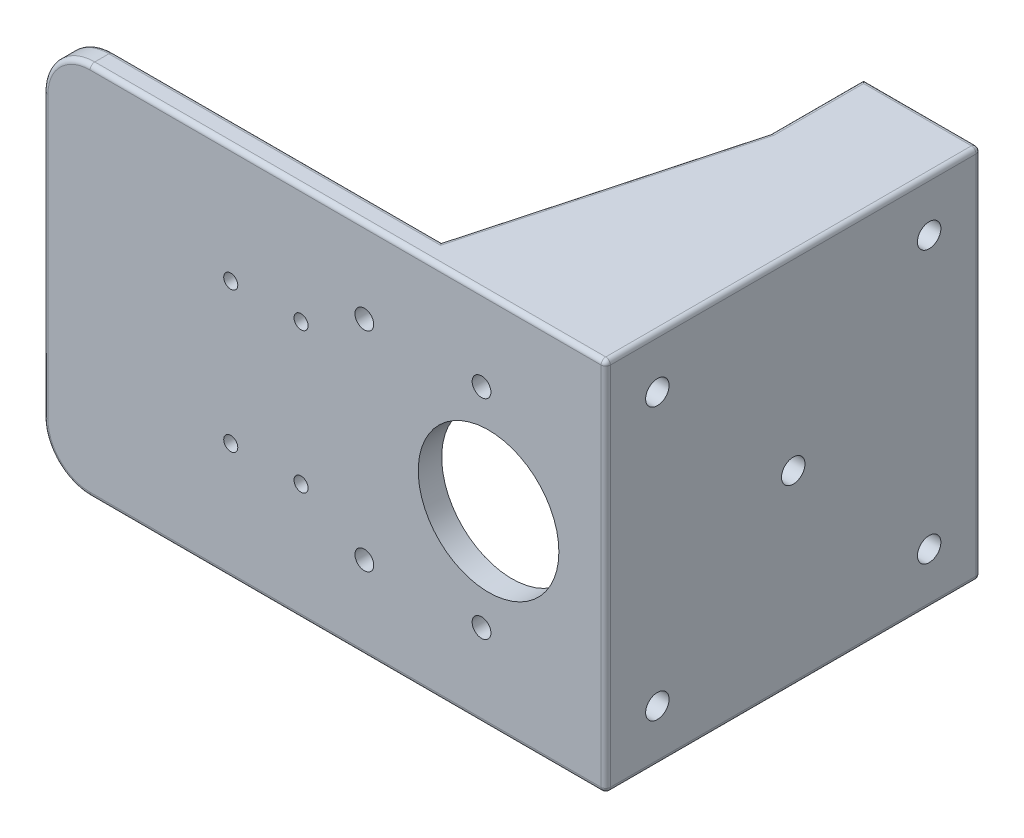
SolidWorks part; units mm, degrees
ref_plane "前视基准面" through (0, 0, 0) normal (0, 0, 1) x (1, 0, 0)
ref_plane "上视基准面" through (0, 0, 0) normal (0, 1, 0) x (1, 0, 0)
ref_plane "右视基准面" through (0, 0, 0) normal (1, 0, 0) x (0, 0, -1)
sketch "草图1" plane through (0, 0, 0) normal (0, 0, 1) x (1, 0, 0)
  line L1 (60, -40) -> (-60, -40)
  line L2 (60, -40) -> (60, 40)
  line L3 (60, 40) -> (-60, 40)
  line L4 (-60, -40) -> (-60, 40)
  line L5 (60, -40) -> (-60, 40) construction
  line L6 (60, 40) -> (-60, -40) construction
  point P0 (0, 0)
  dimension "D1" = 80
  dimension "D2" = 120
extrude "凸台-拉伸1" add sketch "草图1" along normal blind 5
sketch "草图3" plane through (0, 0, 5) normal (0, 0, 1) x (1, 0, 0)
  circle A0 centre (-45, 0) radius 4
  dimension "D2" = 8
extrude "切除-拉伸2" cut sketch "草图3" against normal blind 10
sketch "草图4" plane through (0, 0, 5) normal (0, 0, 1) x (1, 0, 0)
  line L1 (102, -10) -> (14, -10)
  line L2 (102, -10) -> (102, 10)
  line L3 (102, 10) -> (14, 10)
  line L4 (14, -10) -> (14, 10)
  line L5 (102, -10) -> (14, 10) construction
  line L6 (102, 10) -> (14, -10) construction
  line L7 (-60, 40) -> (-60, -40) construction
  point P0 (58, 0)
  dimension "D1" = 162
  dimension "D2" = 20
  dimension "D3" = 88
extrude "凸台-拉伸2" [suppressed] add sketch "草图4" along normal blind 10
sketch "草图5" plane through (0, 0, 5) normal (0, 0, 1) x (1, 0, 0)
  line L0 (60, -40) -> (60, 40) construction
  circle A0 centre (35, 0) radius 15
  dimension "D1" = 30
  dimension "D2" = 25
extrude "切除-拉伸3" cut sketch "草图5" against normal blind 10
sketch "草图10" [suppressed] plane through (0, 0, 15) normal (0, 0, 1) x (1, 0, 0)
  line L0 (14, 0) -> (102, 0) construction
  line L1 (14, 10) -> (14, -10) construction
  line L2 (102, -10) -> (102, 10) construction
  line L3 (14, 5.1) -> (102, 5.1)
  line L4 (14, -5.1) -> (102, -5.1)
  arc A0 (14, 5.1) -> (14, -5.1) centre (14, 0) ccw
  arc A1 (102, -5.1) -> (102, 5.1) centre (102, 0) ccw
  point P6 (58, 0)
  dimension "D1" = 5.1
extrude "切除-拉伸4" [suppressed] cut sketch "草图10" against normal blind 7
hole_wizard "Ø4.0mm 暗销孔1" positions "草图11" profile "草图12" hole size "Ø4.0" standard "GB" end condition through all
sketch "草图11" plane through (0, 0, 0) normal (0, 0, -1) x (-1, 0, 0)
  point P0 (-8.5, -22.25)
  point P3 (-8.5, 22.25)
  point P6 (-33.5, 22.25)
  point P8 (-33.5, -22.25)
sketch "草图12" plane through (8.5, -22.25, 0) normal (1, 0, 0) x (0, 1, 0)
  line L0 (0, 0) -> (0, 5)
  line L1 (0, 5) -> (2, 5)
  line L2 (2, 5) -> (2, 0)
  line L5 (2, 0) -> (0, 0)
  line L11 (0, -6.35) -> (0, 107.95) construction
  dimension "通孔孔直径" = 4
  dimension "通孔孔深度" = 5
fillet "圆角1" radius 10 2 edges at (-60, -40, 2.5) (-60, 40, 2.5)
sketch "草图13" plane through (0, 0, 5) normal (0, 0, 1) x (1, 0, 0)
  circle A0 centre (-45, 0) radius 6.9694
extrude "凸台-拉伸5" add sketch "草图13" against normal blind 5
sketch "草图14" plane through (0, -40, 0) normal (0, -1, 0) x (1, 0, 0)
  line L1 (60, 0) -> (55, 0)
  line L2 (60, 0) -> (60, -75)
  line L3 (60, -75) -> (55, -75)
  line L4 (55, 0) -> (55, -75)
  dimension "D1" = 5
  dimension "D2" = 75
extrude "凸台-拉伸6" add sketch "草图14" against normal up to surface (80 mm away) up to face at (5, 40, 2.5)
sketch "草图15" plane through (0, -40, 0) normal (0, -1, 0) x (1, 0, 0)
  line L1 (55, -75) -> (35, -75)
  line L2 (55, -75) -> (55, -70)
  line L3 (55, -70) -> (35, -70)
  line L4 (35, -75) -> (35, -70)
  dimension "D1" = 5
  dimension "D2" = 20
extrude "凸台-拉伸7" add sketch "草图15" against normal up to surface (80 mm away) up to face at (21.6667, 40, -23.3333)
sketch "草图16" plane through (0, -40, 0) normal (0, -1, 0) x (1, 0, 0)
  line L0 (20, 5) -> (20, 0)
  line L1 (-50, 5) -> (60, 5) construction
  line L2 (-50, 0) -> (55, 0) construction
  line L4 (35, -75) -> (60, -75)
  line L5 (60, -75) -> (60, 5)
  line L6 (60, 5) -> (20, 5)
  line L7 (35, -75) -> (35, -55)
  line L8 (35, -55) -> (20, 0)
  dimension "D1" = 40
  dimension "D2" = 20
extrude "凸台-拉伸8" add sketch "草图16" against normal blind 5
mirror "镜向1" about plane through (0, 0, 0) normal (0, 1, 0) of "凸台-拉伸8"
sketch "草图17" plane through (0, 0, -75) normal (0, 0, -1) x (-1, 0, 0)
  line L0 (-60, 40) -> (-60, -40) construction
  circle A0 centre (-47, -15) radius 3
  circle A1 centre (-47, 15) radius 3
  dimension "D1" = 6
  dimension "D3" = 13
  dimension "D2" = 13
extrude "切除-拉伸5" [suppressed] cut sketch "草图17" against normal blind 5
fillet "圆角2" radius 1 20 edges at (-57.0711, 37.0711, 5) (-57.0711, 37.0711, 0) (-60, 0, 0) (-60, 0, 5) (-57.0711, -37.0711, 5) (-57.0711, -37.0711, 0) (5, 40, 5) (-15, 40, 0) (47.5, 40, -75) (60, 0, -75) (60, 0, 5) (60, 40, -35) (5, -40, 5) (60, -40, -35) (47.5, -40, -75) (-15, -40, 0) (27.5, 40, -27.5) (35, 40, -65) (35, -40, -65) (27.5, -40, -27.5)
fillet "圆角3" [suppressed] radius 1
sketch "草图18" [suppressed] plane through (102, 0, 0) normal (1, 0, 0) x (0, 0, -1)
  line L8 (-15, -6.1) -> (-15, -9)
  line L9 (-14, -10) -> (-5, -10)
  line L10 (-5, -10) -> (-5, 10)
  line L11 (-5, 10) -> (-14, 10)
  line L12 (-15, 9) -> (-15, 6.1)
  line L13 (-14, 5.1) -> (-8, 5.1)
  line L14 (-8, 5.1) -> (-8, -5.1)
  line L15 (-8, -5.1) -> (-14, -5.1)
  line L16 (-15, -6.1) -> (-15, -9)
  line L17 (-14, -10) -> (-5, -10)
  line L19 (-5, 10) -> (-14, 10)
  line L20 (-15, 9) -> (-15, 6.1)
  line L21 (-14, 5.1) -> (-8, 5.1)
  line L22 (-8, 5.1) -> (-8, -5.1)
  line L23 (-8, -5.1) -> (-14, -5.1)
  line L33 (-5, -10) -> (-5, 10)
  arc A4 (-15, -9) -> (-14, -10) centre (-14, -9) ccw
  arc A5 (-14, 10) -> (-15, 9) centre (-14, 9) ccw
  arc A6 (-15, 6.1) -> (-14, 5.1) centre (-14, 6.1) ccw
  arc A7 (-14, -5.1) -> (-15, -6.1) centre (-14, -6.1) ccw
  arc A8 (-15, -9) -> (-14, -10) centre (-14, -9) ccw
  arc A9 (-14, 10) -> (-15, 9) centre (-14, 9) ccw
  arc A10 (-15, 6.1) -> (-14, 5.1) centre (-14, 6.1) ccw
  arc A11 (-14, -5.1) -> (-15, -6.1) centre (-14, -6.1) ccw
  dimension "D1" = 0
extrude "切除-拉伸6" [suppressed] cut sketch "草图18" against normal blind 100
hole_wizard "Ø3.0mm 暗销孔1" positions "草图19" profile "草图20" hole size "Ø3.0" standard "GB"
sketch "草图19" plane through (0, 0, 5) normal (0, 0, 1) x (1, 0, 0)
  point P0 (-5, -15)
  point P3 (-5, 15)
  point P6 (-20, 15)
  point P9 (-20, -15)
sketch "草图20" plane through (-5, -15, 5) normal (1, 0, 0) x (0, -1, 0)
  line L0 (0, 0) -> (0, 8.4013)
  line L1 (0, 8.4013) -> (1.5, 7.5)
  line L2 (1.5, 7.5) -> (1.5, 0)
  line L5 (1.5, 0) -> (0, 0)
  line L10 (0, 8.4013) -> (-1.5, 7.5) construction
  line L11 (0, -6.35) -> (0, 107.95) construction
  dimension "孔直径" = 3
  dimension "孔深度" = 7.5
  dimension "导头角度" = 118
sketch "草图21" plane through (60, 0, 0) normal (1, 0, 0) x (0, 0, -1)
  line L0 (35, 40) -> (35, -40) construction
  line L1 (-4, 40) -> (74, 40) construction
  line L2 (74, -40) -> (-4, -40) construction
  circle A0 centre (35, 0) radius 2.5
  dimension "D1" = 5
extrude "切除-拉伸7" cut sketch "草图21" against normal blind 10
sketch "草图22" plane through (60, 0, 0) normal (1, 0, 0) x (0, 0, -1)
  line L0 (6.0086, 28.9914) -> (35, 0) construction
  line L1 (35, 0) -> (35, 41) construction
  circle A0 centre (35, 0) radius 41 construction
  dimension "D1" = 82
  dimension "D2" = 45
hole_wizard "Ø5.0mm 暗销孔1" positions "草图23" profile "草图24" hole size "Ø5.0" standard "GB"
sketch "草图23" plane through (60, 0, 0) normal (1, 0, 0) x (0, 0, -1)
  point P0 (6.0086, 28.9914)
sketch "草图24" plane through (60, 28.9914, -6.0086) normal (0, 1, 0) x (0, 0, -1)
  line L0 (0, 0) -> (0, 13.9022)
  line L1 (0, 13.9022) -> (2.5, 12.4)
  line L2 (2.5, 12.4) -> (2.5, 0)
  line L5 (2.5, 0) -> (0, 0)
  line L10 (0, 13.9022) -> (-2.5, 12.4) construction
  line L11 (0, -6.35) -> (0, 107.95) construction
  dimension "孔直径" = 5
  dimension "孔深度" = 12.4
  dimension "导头角度" = 118
pattern_circular "阵列(圆周)1" count 4 over 360 about axis through (0, 0, -35) along (1, 0, 0) of "Ø5.0mm 暗销孔1"
